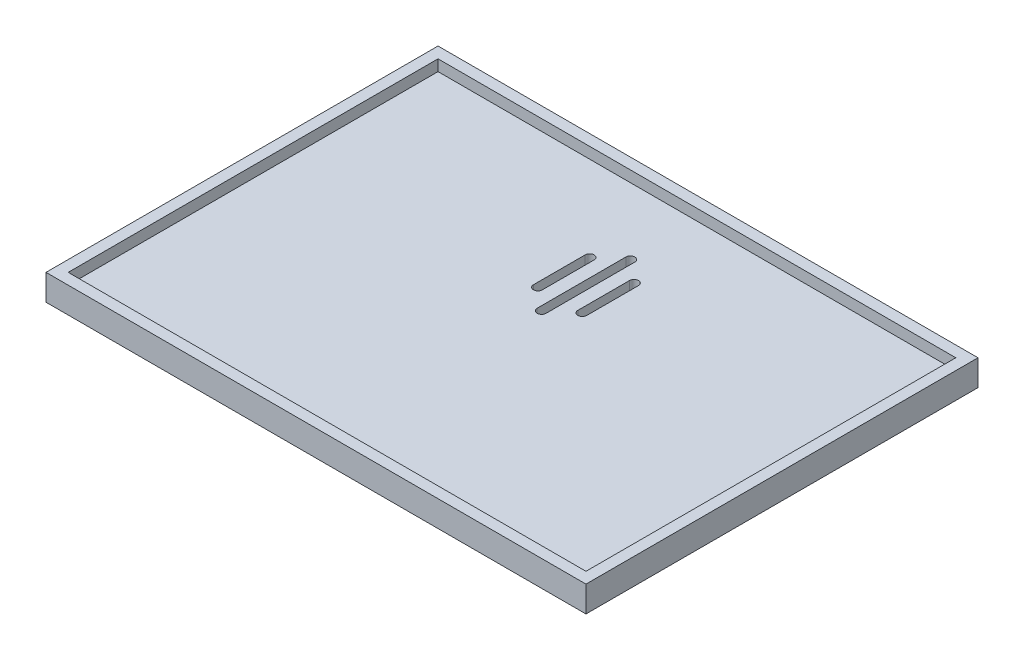
SolidWorks part; units mm, degrees
ref_plane "Front Plane" through (0, 0, 0) normal (0, 0, 1) x (1, 0, 0)
ref_plane "Top Plane" through (0, 0, 0) normal (0, 1, 0) x (1, 0, 0)
ref_plane "Right Plane" through (0, 0, 0) normal (1, 0, 0) x (0, 0, -1)
sketch "Sketch1" plane through (0, 0, 0) normal (0, 1, 0) x (1, 0, 0)
  line L1 (-36.5, 26.5) -> (36.5, 26.5)
  line L2 (-36.5, 26.5) -> (-36.5, -26.5)
  line L3 (-36.5, -26.5) -> (36.5, -26.5)
  line L4 (36.5, 26.5) -> (36.5, -26.5)
  point P4 (0, 26.5)
  point P6 (36.5, 0)
  dimension "D1" = 73
  dimension "D2" = 53
extrude "Boss-Extrude1" add sketch "Sketch1" along normal blind 2
sketch "Sketch2" plane through (0, 2, 0) normal (0, 1, 0) x (1, 0, 0)
  line L1 (-36.5, 26.5) -> (36.5, 26.5)
  line L2 (-36.5, 26.5) -> (-36.5, -26.5)
  line L3 (-36.5, -26.5) -> (36.5, -26.5)
  line L4 (36.5, 26.5) -> (36.5, -26.5)
  line L5 (-35, 25) -> (35, 25)
  line L6 (-35, 25) -> (-35, -25)
  line L7 (-35, -25) -> (35, -25)
  line L8 (35, 25) -> (35, -25)
  dimension "D1" = 1.5
  dimension "D2" = 1.5
  dimension "D3" = 1.5
  dimension "D4" = 1.5
extrude "Boss-Extrude2" add sketch "Sketch2" along normal blind 1.5
sketch "Sketch3" plane through (0, 0, 0) normal (0, -1, 0) x (1, 0, 0)
  line L0 (0, -4) -> (0, -16) construction
  line L1 (0.6, -4) -> (0.6, -16)
  line L2 (-0.6, -4) -> (-0.6, -16)
  line L3 (3, -6.5) -> (3, -13.5) construction
  line L4 (3.6, -6.5) -> (3.6, -13.5)
  line L5 (2.4, -6.5) -> (2.4, -13.5)
  line L6 (-3, -6.5) -> (-3, -13.5) construction
  line L7 (-2.4, -6.5) -> (-2.4, -13.5)
  line L8 (-3.6, -6.5) -> (-3.6, -13.5)
  arc A0 (0.6, -4) -> (-0.6, -4) centre (0, -4) ccw
  arc A1 (-0.6, -16) -> (0.6, -16) centre (0, -16) ccw
  arc A2 (3.6, -6.5) -> (2.4, -6.5) centre (3, -6.5) ccw
  arc A3 (2.4, -13.5) -> (3.6, -13.5) centre (3, -13.5) ccw
  arc A4 (-2.4, -6.5) -> (-3.6, -6.5) centre (-3, -6.5) ccw
  arc A5 (-3.6, -13.5) -> (-2.4, -13.5) centre (-3, -13.5) ccw
  point P3 (0, -10)
  point P8 (3, -10)
  point P15 (-3, -10)
  point P22 (0, 0)
  point P23 (0, 0)
  dimension "D1" = 1.2
  dimension "D2" = 1.2
  dimension "D3" = 1.2
  dimension "D4" = 3
  dimension "D5" = 3
  dimension "D6" = 7
  dimension "D7" = 7
  dimension "D8" = 10
  dimension "D9" = 12
extrude "Cut-Extrude1" cut sketch "Sketch3" against normal through all
